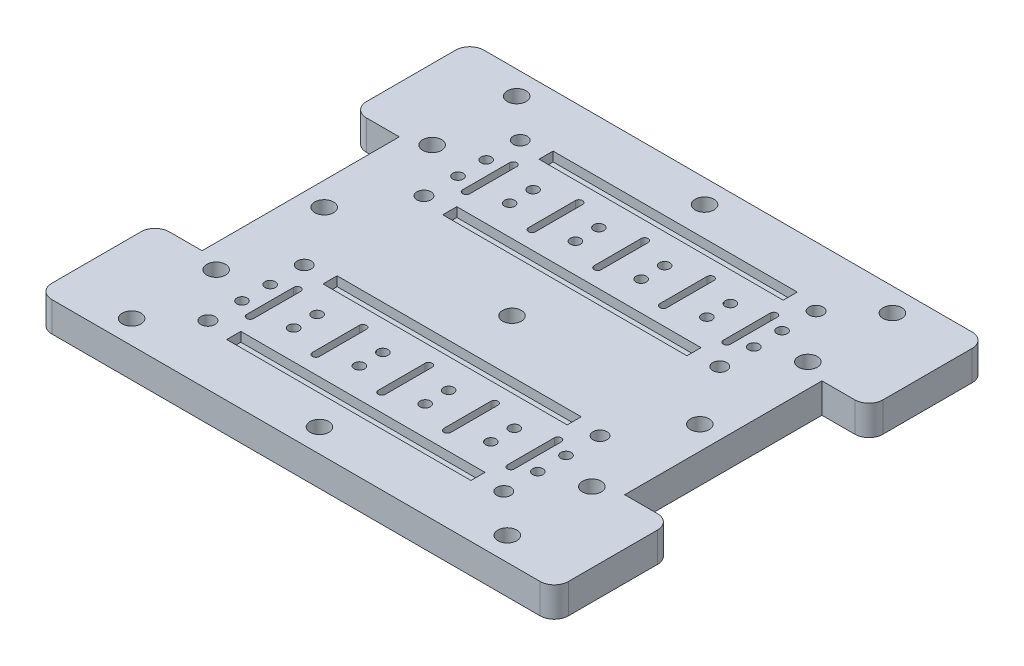
SolidWorks part; units mm, degrees
material "Acrylic (Medium-high impact)"
ref_plane "Front Plane" through (0, 0, 0) normal (0, 0, 1) x (1, 0, 0)
ref_plane "Top Plane" through (0, 0, 0) normal (0, 1, 0) x (1, 0, 0)
ref_plane "Right Plane" through (0, 0, 0) normal (1, 0, 0) x (0, 0, -1)
sketch "Sketch1" plane through (0, 0, 0) normal (0, 1, 0) x (1, 0, 0)
  line L0 (45, 46) -> (45, 0) construction
  line L1 (0, 0) -> (90, 0)
  line L2 (0, 0) -> (0, 46)
  line L3 (0, 46) -> (90, 46)
  line L4 (90, 0) -> (90, 46)
  line L5 (0, 23) -> (5, 23) construction
  line L6 (90, 23) -> (85, 23) construction
  circle A1 centre (45, 5) radius 2
  circle A2 centre (5, 23) radius 2
  circle A3 centre (85, 23) radius 2
  dimension "D3" = 4
  dimension "D4" = 4
  dimension "D7" = 4
  dimension "D1" = 90
  dimension "D2" = 46
  dimension "D5" = 5
  dimension "D6" = 5
extrude "Boss-Extrude1" add sketch "Sketch1" along normal blind 6.35
sketch "Sketch2" plane through (0, 6.35, 0) normal (0, 1, 0) x (1, 0, 0)
  line L0 (5, 41) -> (0, 46)
  line L1 (5, 41) -> (85, 41)
  line L2 (5, 41) -> (5, 5)
  line L3 (5, 5) -> (85, 5)
  line L4 (85, 41) -> (85, 5)
  line L5 (85, 41) -> (90, 46)
  line L6 (5, 5) -> (0, 0)
  line L7 (85, 5) -> (90, 0)
  line L8 (5, 41) -> (5, 46)
  line L9 (90, 46) -> (0, 46) construction
  line L10 (5, 41) -> (0, 41)
  line L11 (0, 46) -> (0, 0) construction
  dimension "D1" = 5
sketch "Sketch5" plane through (0, 6.35, 0) normal (0, 1, 0) x (1, 0, 0)
  line L0 (80, 36) -> (90, 36)
  line L1 (10, 10) -> (80, 10)
  line L2 (10, 10) -> (10, 36)
  line L3 (10, 36) -> (80, 36)
  line L4 (80, 10) -> (80, 36)
  line L5 (90, 0) -> (90, 46) construction
  line L6 (10, 10) -> (0, 10)
  line L7 (0, 46) -> (0, 0) construction
  line L8 (10, 36) -> (10, 46)
  line L9 (90, 46) -> (0, 46) construction
  line L10 (80, 10) -> (80, 0)
  line L11 (0, 0) -> (90, 0) construction
  line L12 (10, 23) -> (80, 23)
  line L13 (45, 23) -> (45, 36)
  line L14 (24, 25.5) -> (24, 20.5)
  line L15 (24, 20.5) -> (38, 20.5)
  line L16 (38, 20.5) -> (38, 25.5)
  line L17 (38, 25.5) -> (52, 25.5)
  line L18 (52, 25.5) -> (52, 20.5)
  line L19 (52, 20.5) -> (66, 20.5)
  line L20 (66, 20.5) -> (66, 25.5)
  line L21 (13.5, 26) -> (13.5, 20)
  line L22 (13.5, 26) -> (45, 26)
  line L23 (45, 26) -> (76.5, 26)
  line L24 (76.5, 26) -> (76.5, 20)
  point P23 (38, 23)
  point P29 (45, 25.5)
  point P32 (76.5, 23)
  point P33 (13.5, 23)
  dimension "D1" = 70
  dimension "D2" = 26
  dimension "D3" = 5
  dimension "D4" = 14
  dimension "D5" = 6
  dimension "D6" = 10.5
hole_wizard "M2 Clearance Hole1" positions "Sketch3" profile "Sketch4" hole size "M2" standard "ANSI Metric" end condition through all
sketch "Sketch3" plane through (0, 6.35, 0) normal (0, 1, 0) x (1, 0, 0)
  point P12 (13.5, 26)
  point P15 (13.5, 20)
  point P18 (24, 25.5)
  point P21 (24, 20.5)
  point P24 (38, 25.5)
  point P27 (38, 20.5)
  point P30 (52, 25.5)
  point P33 (52, 20.5)
  point P36 (66, 25.5)
  point P39 (66, 20.5)
  point P42 (76.5, 26)
  point P45 (76.5, 20)
sketch "Sketch4" plane through (13.5, 6.35, -26) normal (1, 0, 0) x (0, 0, 1)
  line L0 (0, 0) -> (0, 6.35)
  line L1 (0, 6.35) -> (1.1, 6.35)
  line L2 (1.1, 6.35) -> (1.1, 0)
  line L5 (1.1, 0) -> (0, 0)
  line L11 (0, -6.35) -> (0, 107.95) construction
  dimension "Thru Hole Dia." = 2.2
  dimension "Thru Hole Depth" = 6.35
sketch "Sketch6" plane through (0, 6.35, 0) normal (0, 1, 0) x (1, 0, 0)
  line L0 (13.5, 28.5) -> (13.5, 32.25) construction
  line L1 (13.5, 32.25) -> (20.5, 32.25) construction
  line L2 (20.5, 32.25) -> (27.5, 32.25) construction
  line L3 (27.5, 32.25) -> (34.5, 32.25) construction
  line L4 (34.5, 32.25) -> (41.5, 32.25) construction
  line L5 (41.5, 32.25) -> (48.5, 32.25) construction
  line L6 (48.5, 32.25) -> (55.5, 32.25) construction
  line L7 (55.5, 32.25) -> (62.5, 32.25) construction
  line L8 (62.5, 32.25) -> (69.5, 32.25) construction
  line L9 (69.5, 32.25) -> (76.5, 32.25) construction
  line L10 (76.5, 32.25) -> (76.5, 26) construction
  line L11 (10, 36) -> (10, 46) construction
  line L12 (10, 36) -> (80, 36) construction
  line L13 (10, 36) -> (10, 10) construction
  line L14 (10, 10) -> (80, 10) construction
  line L15 (80, 36) -> (80, 10) construction
  line L16 (90, 46) -> (0, 46) construction
  line L17 (10, 36) -> (0, 36) construction
  line L18 (0, 46) -> (0, 0) construction
  line L19 (80, 0) -> (80, 10) construction
  line L20 (0, 0) -> (90, 0) construction
  line L21 (90, 10) -> (80, 10) construction
  line L22 (90, 0) -> (90, 46) construction
  line L23 (13.5, 26) -> (13.5, 28.5) construction
  line L24 (13.5, 32.25) -> (13.5, 36) construction
  line L25 (13.5, 10) -> (13.5, 13.75) construction
  line L26 (13.5, 13.75) -> (20.5, 13.75) construction
  line L27 (20.5, 13.75) -> (27.5, 13.75) construction
  line L28 (27.5, 13.75) -> (34.5, 13.75) construction
  line L29 (34.5, 13.75) -> (41.5, 13.75) construction
  line L30 (41.5, 13.75) -> (48.5, 13.75) construction
  line L31 (48.5, 13.75) -> (55.5, 13.75) construction
  line L32 (55.5, 13.75) -> (62.5, 13.75) construction
  line L33 (62.5, 13.75) -> (69.5, 13.75) construction
  line L34 (69.5, 13.75) -> (76.5, 13.75) construction
  line L35 (76.5, 13.75) -> (76.5, 20) construction
  line L36 (14.6, 26) -> (75.4, 26) construction
  line L37 (14.6, 20) -> (75.4, 20) construction
  line L38 (45, 32.25) -> (45, 26) construction
  line L39 (59, 32.25) -> (59, 26) construction
  line L40 (59, 13.75) -> (59, 20) construction
  line L41 (45, 13.75) -> (45, 20) construction
  line L42 (17.25, 28) -> (17.25, 18) construction
  line L43 (18, 28) -> (18, 18)
  line L44 (16.5, 28) -> (16.5, 18)
  line L45 (13.5, 20) -> (13.5, 26) construction
  line L48 (24, 25.5) -> (24, 20.5) construction
  circle A1 centre (76.5, 26) radius 1.1 construction
  circle A21 centre (13.5, 26) radius 1.1 construction
  circle A22 centre (13.5, 20) radius 1.1 construction
  circle A23 centre (76.5, 20) radius 1.1 construction
  arc A24 (18, 28) -> (16.5, 28) centre (17.25, 28) ccw
  arc A25 (16.5, 18) -> (18, 18) centre (17.25, 18) ccw
  point P87 (17.25, 23)
  point P95 (13.5, 23)
  point P101 (45, 32.25)
  point P103 (45, 26)
  point P105 (45, 20)
  point P108 (45, 13.75)
  dimension "D6" = 0.75
  dimension "D2" = 10
  dimension "D3" = 2.5
  dimension "D5" = 10
  dimension "D7" = 6.75
extrude "Cut-Extrude1" cut sketch "Sketch6" against normal through all
sketch "Sketch7" plane through (0, 6.35, 0) normal (0, 1, 0) x (1, 0, 0)
  line L0 (30.75, 28) -> (30.75, 18) construction
  line L1 (31.5, 28) -> (31.5, 18)
  line L2 (30, 28) -> (30, 18)
  line L3 (5, 23) -> (85, 23) construction
  line L4 (44, 28) -> (44, 18)
  line L5 (45.5, 28) -> (45.5, 18)
  line L6 (44.75, 28) -> (44.75, 18) construction
  line L7 (58, 28) -> (58, 18)
  line L8 (59.5, 28) -> (59.5, 18)
  line L9 (58.75, 28) -> (58.75, 18) construction
  line L10 (72.75, 28) -> (72.75, 18) construction
  line L11 (73.5, 28) -> (73.5, 18)
  line L12 (72, 28) -> (72, 18)
  arc A0 (31.5, 28) -> (30, 28) centre (30.75, 28) ccw
  arc A1 (30, 18) -> (31.5, 18) centre (30.75, 18) ccw
  arc A2 (18, 28) -> (16.5, 28) centre (17.25, 28) ccw construction
  arc A3 (16.5, 18) -> (18, 18) centre (17.25, 18) ccw construction
  arc A4 (45.5, 28) -> (44, 28) centre (44.75, 28) ccw
  arc A5 (44, 18) -> (45.5, 18) centre (44.75, 18) ccw
  arc A6 (59.5, 28) -> (58, 28) centre (58.75, 28) ccw
  arc A7 (58, 18) -> (59.5, 18) centre (58.75, 18) ccw
  arc A8 (73.5, 28) -> (72, 28) centre (72.75, 28) ccw
  arc A9 (72, 18) -> (73.5, 18) centre (72.75, 18) ccw
  point P2 (30.75, 23)
  point P15 (17.25, 28.75)
  point P16 (30.75, 28.75)
  point P20 (17.25, 17.25)
  point P21 (30.75, 17.25)
  point P25 (44.75, 23)
  point P32 (58.75, 23)
  point P38 (72.75, 23)
  dimension "D1" = 13.5
  dimension "D3" = 14
  dimension "D4" = 2
  dimension "D5" = 14
  dimension "D2" = 3
extrude "Cut-Extrude2" cut sketch "Sketch7" against normal through all
ref_plane "Plane1" through (0, 0, -46) normal (0, 0, -1) x (-1, 0, 0)
mirror "Mirror1" about plane through (0, 0, -46) normal (0, 0, -1) of "Boss-Extrude1", "M2 Clearance Hole1", "Cut-Extrude1", "Cut-Extrude2"
sketch "Sketch8" plane through (90, 0, 0) normal (1, 0, 0) x (0, 0, -1)
  line L0 (0, 6.35) -> (92, 6.35) construction
  line L1 (25, 6.35) -> (0, 6.35)
  line L2 (25, 6.35) -> (25, 0)
  line L3 (25, 0) -> (0, 0)
  line L4 (0, 6.35) -> (0, 0)
  line L5 (25, 6.35) -> (0, 0) construction
  line L6 (25, 0) -> (0, 6.35) construction
  line L8 (67, 0) -> (92, 0)
  line L9 (67, 0) -> (67, 6.35)
  line L10 (67, 6.35) -> (92, 6.35)
  line L11 (92, 0) -> (92, 6.35)
  line L12 (67, 0) -> (92, 6.35) construction
  line L13 (67, 6.35) -> (92, 0) construction
  point P0 (12.5, 3.175)
  point P8 (79.5, 3.175)
  dimension "D1" = 25
extrude "Boss-Extrude2" add sketch "Sketch8" along normal blind 10
fillet "Fillet1" radius 3 4 edges at (100, 3.175, -92) (100, 3.175, -67) (100, 3.175, 0) (100, 3.175, -25)
ref_plane "Plane2" through (45, 0, 0) normal (-1, 0, 0) x (0, 0, 1)
mirror "Mirror5" about plane through (45, 0, 0) normal (-1, 0, 0) of "Boss-Extrude1", "Fillet1", "Boss-Extrude2", "Mirror1"
sketch "Sketch9" plane through (0, 6.35, 0) normal (0, 1, 0) x (1, 0, 0)
  line L5 (45, 87) -> (5, 87) construction
  line L6 (45, 87) -> (85, 87) construction
  line L7 (45, 5) -> (5, 5) construction
  line L8 (45, 5) -> (85, 5) construction
  circle A10 centre (5, 5) radius 2
  circle A11 centre (85, 5) radius 2
  circle A12 centre (85, 87) radius 2
  circle A13 centre (5, 87) radius 2
  dimension "D1" = 4
  dimension "D2" = 4
  dimension "D3" = 4
  dimension "D4" = 4
extrude "Cut-Extrude3" cut sketch "Sketch9" against normal blind 10
sketch "Sketch10" plane through (0, 0, 0) normal (0, -1, 0) x (1, 0, 0)
  circle A0 centre (85, -46) radius 2 construction
  circle A1 centre (45, -46) radius 2 construction
  circle A2 centre (5, -46) radius 2 construction
  circle A3 centre (85, -46) radius 2
  circle A4 centre (45, -46) radius 2
  circle A5 centre (5, -46) radius 2
  dimension "D1" = 4
extrude "Cut-Extrude4" cut sketch "Sketch10" against normal blind 6.35
sketch "Sketch11" plane through (0, 6.35, 0) normal (0, 1, 0) x (1, 0, 0)
  line L0 (55, 46) -> (-55, 46) construction
  line L1 (19, 11.25) -> (71, 11.25)
  line L2 (19, 11.25) -> (19, 14.25)
  line L3 (19, 14.25) -> (71, 14.25)
  line L4 (71, 11.25) -> (71, 14.25)
  line L5 (-7, 0) -> (97, 0) construction
  line L11 (19, 31.75) -> (71, 31.75)
  line L12 (19, 31.75) -> (19, 34.75)
  line L13 (19, 34.75) -> (71, 34.75)
  line L14 (71, 31.75) -> (71, 34.75)
  line L15 (19, 57.25) -> (71, 57.25)
  line L16 (71, 60.25) -> (71, 57.25)
  line L17 (19, 60.25) -> (71, 60.25)
  line L18 (19, 60.25) -> (19, 57.25)
  line L19 (19, 77.75) -> (71, 77.75)
  line L20 (71, 80.75) -> (71, 77.75)
  line L21 (19, 80.75) -> (71, 80.75)
  line L22 (19, 80.75) -> (19, 77.75)
  arc A0 (46, 28) -> (44.5, 28) centre (45.25, 28) ccw construction
  arc A2 (44.5, 18) -> (46, 18) centre (45.25, 18) ccw construction
  point P7 (45.25, 17.25)
  point P9 (45, 11.25)
  point P14 (45, 0)
  point P25 (45.25, 28.75)
  point P26 (45, 14.25)
  point P27 (45, 31.75)
  dimension "D1" = 52
  dimension "D2" = 3
  dimension "D3" = 3
  dimension "D4" = 3
  dimension "D5" = 3
  dimension "D6" = 52
sketch "Sketch12" plane through (0, 6.35, 0) normal (0, 1, 0) x (1, 0, 0)
  line L0 (16.5, 18) -> (16.5, 28) construction
  line L1 (55, 46) -> (-55, 46) construction
  line L3 (19, 31.75) -> (71, 31.75)
  line L4 (19, 31.75) -> (19, 34.75)
  line L5 (19, 34.75) -> (71, 34.75)
  line L6 (71, 31.75) -> (71, 34.75)
  line L7 (-7, 0) -> (97, 0) construction
  line L8 (19, 57.25) -> (71, 57.25)
  line L9 (71, 60.25) -> (71, 57.25)
  line L10 (19, 60.25) -> (71, 60.25)
  line L11 (19, 60.25) -> (19, 57.25)
  line L14 (45, 3.4925) -> (45, -3.4925) construction
  circle A0 centre (13.5, 12.75) radius 1.5
  arc A4 (60, 28) -> (58.5, 28) centre (59.25, 28) ccw construction
  circle A5 centre (13.5, 33.25) radius 1.5
  arc A6 (18, 28) -> (16.5, 28) centre (17.25, 28) ccw construction
  arc A7 (16.5, 18) -> (18, 18) centre (17.25, 18) ccw construction
  circle A8 centre (76.5, 33.25) radius 1.5
  circle A9 centre (76.5, 12.75) radius 1.5
  point P15 (45, 31.75)
  point P16 (59.25, 28.75)
  point P20 (45, 0)
  point P28 (17.25, 28.75)
  point P32 (17.25, 17.25)
  dimension "D1" = 3
  dimension "D2" = 3
  dimension "D5" = 3
  dimension "D6" = 3
  dimension "D3" = 52
  dimension "D4" = 3
  dimension "D7" = 3
  dimension "D8" = 4.5
  dimension "D9" = 4.5
extrude "Cut-Extrude6" cut sketch "Sketch12" against normal through all contours A0 | A5 | A9 | A8
mirror "Mirror7" about plane through (0, 0, -46) normal (0, 0, -1) of "Cut-Extrude6"
extrude "Cut-Extrude7" cut sketch "Sketch11" against normal blind 2
equation "\"wall\"= 10"
equation "\"D1@Sketch1\"=70.00mm+2*\"wall\""
equation "\"D2@Sketch1\"=26mm+2*\"wall\""
equation "\"thick\"=6.35"
equation "\"D1@Boss-Extrude1\"=\"thick\""
